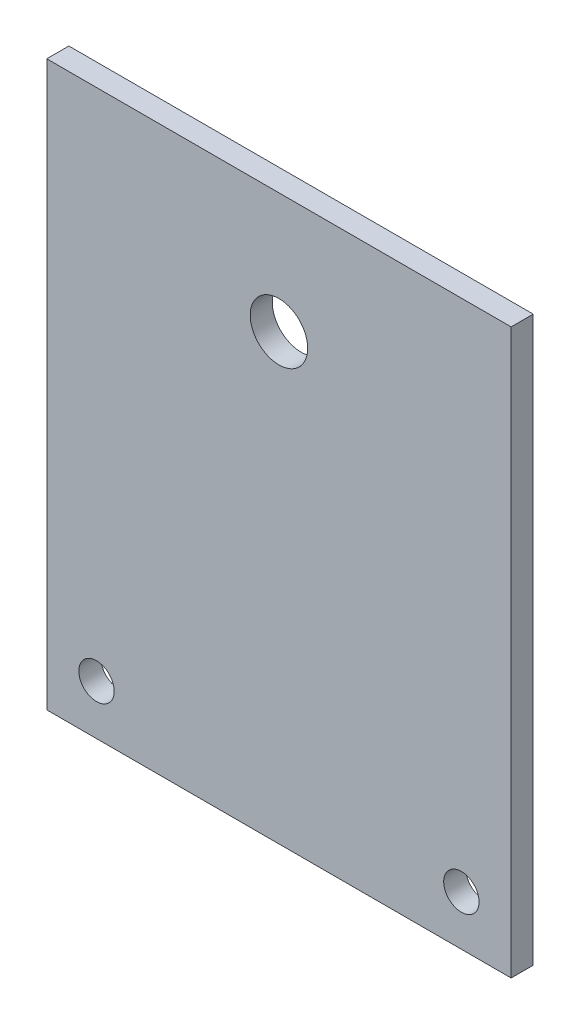
SolidWorks part; units mm, degrees
material "1060 合金"
ref_plane "正面" through (0, 0, 0) normal (0, 0, 1) x (1, 0, 0)
ref_plane "平面" through (0, 0, 0) normal (0, 1, 0) x (1, 0, 0)
ref_plane "右側面" through (0, 0, 0) normal (1, 0, 0) x (0, 0, -1)
sketch "ｽｹｯﾁ1" plane through (0, 0, 0) normal (0, 0, 1) x (1, 0, 0)
  line L1 (-21, 25.5) -> (21, 25.5)
  line L2 (-21, 25.5) -> (-21, -25.5)
  line L3 (-21, -25.5) -> (21, -25.5)
  line L4 (21, 25.5) -> (21, -25.5)
  line L5 (-21, 25.5) -> (21, -25.5) construction
  line L6 (-21, -25.5) -> (21, 25.5) construction
  circle A0 centre (-16.5, -21) radius 1.6
  circle A1 centre (16.5, -21) radius 1.6
  circle A2 centre (0, 14.62) radius 2.6
  point P0 (0, 0)
  point P10 (0, 25.5)
  dimension "D3" = 3.2
  dimension "D4" = 4.5
  dimension "D5" = 4.5
  dimension "D6" = 33
  dimension "D7" = 5.2
  dimension "D8" = 10.88
  dimension "D1" = 42
  dimension "D2" = 51
  dimension "D9" = 40.12
extrude "ﾎﾞｽ - 押し出し1" add sketch "ｽｹｯﾁ1" along normal blind 2
